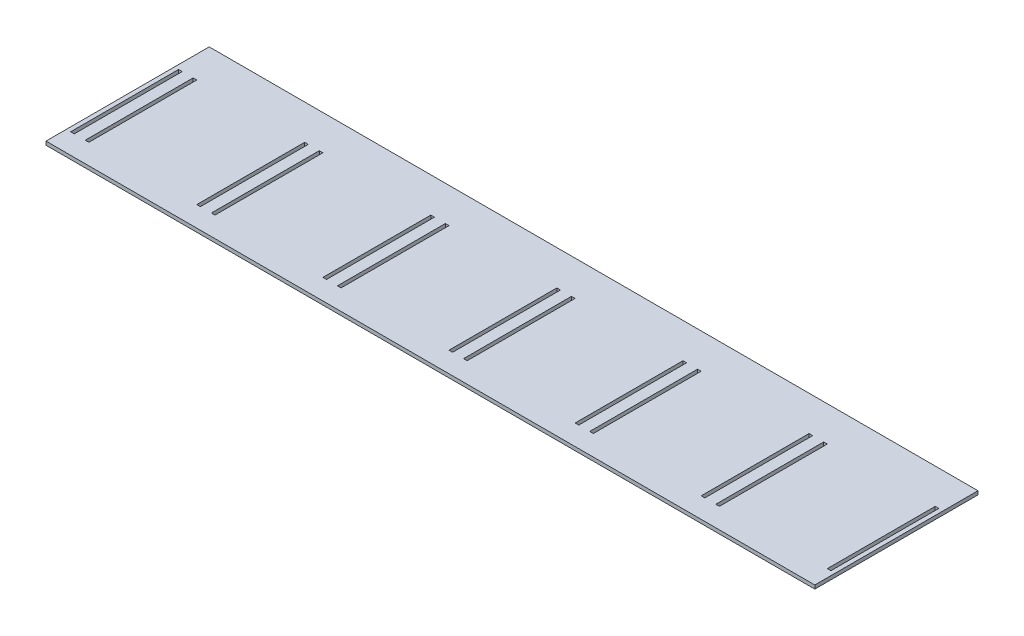
SolidWorks part; units mm, degrees
ref_plane "Front Plane" through (0, 0, 0) normal (0, 0, 1) x (1, 0, 0)
ref_plane "Top Plane" through (0, 0, 0) normal (0, 1, 0) x (1, 0, 0)
ref_plane "Right Plane" through (0, 0, 0) normal (1, 0, 0) x (0, 0, -1)
sketch "Sketch2" plane through (0, 0, 0) normal (0, 1, 0) x (1, 0, 0)
  line L0 (72.7165, -41.1648) -> (74.7165, -41.1648)
  line L2 (70.3665, 37.5852) -> (70.3665, -52.4148)
  line L3 (142.2665, 18.3352) -> (144.2665, 18.3352)
  line L4 (70.3665, 37.5852) -> (494.3665, 37.5852)
  line L5 (70.3665, 41.5852) -> (70.3665, -52.4148) construction
  line L6 (74.7165, 18.3352) -> (74.7165, -41.1648)
  line L7 (142.2665, 18.3352) -> (142.2665, -41.1648)
  line L8 (82.7665, 18.3352) -> (82.7665, -41.1648)
  line L9 (72.7165, 18.3352) -> (74.7165, 18.3352)
  line L10 (80.7665, 18.3352) -> (82.7665, 18.3352)
  line L11 (494.3665, 37.5852) -> (494.3665, -52.4148)
  line L12 (80.7665, -41.1648) -> (82.7665, -41.1648)
  line L13 (144.2665, 18.3352) -> (144.2665, -41.1648)
  line L14 (80.7665, 18.3352) -> (80.7665, -41.1648)
  line L15 (142.2665, -41.1648) -> (144.2665, -41.1648)
  line L16 (150.3165, -41.1648) -> (152.3165, -41.1648)
  line L17 (150.3165, 18.3352) -> (150.3165, -41.1648)
  line L18 (152.3165, 18.3352) -> (152.3165, -41.1648)
  line L19 (150.3165, 18.3352) -> (152.3165, 18.3352)
  line L20 (211.8165, 18.3352) -> (213.8165, 18.3352)
  line L21 (211.8165, 18.3352) -> (211.8165, -41.1648)
  line L22 (213.8165, 18.3352) -> (213.8165, -41.1648)
  line L23 (211.8165, -41.1648) -> (213.8165, -41.1648)
  line L24 (219.8665, -41.1648) -> (221.8665, -41.1648)
  line L25 (219.8665, 18.3352) -> (219.8665, -41.1648)
  line L26 (221.8665, 18.3352) -> (221.8665, -41.1648)
  line L27 (219.8665, 18.3352) -> (221.8665, 18.3352)
  line L28 (281.3665, 18.3352) -> (283.3665, 18.3352)
  line L29 (281.3665, 18.3352) -> (281.3665, -41.1648)
  line L30 (283.3665, 18.3352) -> (283.3665, -41.1648)
  line L31 (281.3665, -41.1648) -> (283.3665, -41.1648)
  line L32 (289.4165, -41.1648) -> (291.4165, -41.1648)
  line L33 (289.4165, 18.3352) -> (289.4165, -41.1648)
  line L34 (291.4165, 18.3352) -> (291.4165, -41.1648)
  line L35 (289.4165, 18.3352) -> (291.4165, 18.3352)
  line L36 (350.9165, 18.3352) -> (352.9165, 18.3352)
  line L37 (350.9165, 18.3352) -> (350.9165, -41.1648)
  line L38 (352.9165, 18.3352) -> (352.9165, -41.1648)
  line L39 (350.9165, -41.1648) -> (352.9165, -41.1648)
  line L40 (358.9665, -41.1648) -> (360.9665, -41.1648)
  line L41 (358.9665, 18.3352) -> (358.9665, -41.1648)
  line L42 (360.9665, 18.3352) -> (360.9665, -41.1648)
  line L43 (358.9665, 18.3352) -> (360.9665, 18.3352)
  line L44 (420.4665, 18.3352) -> (422.4665, 18.3352)
  line L45 (420.4665, 18.3352) -> (420.4665, -41.1648)
  line L46 (422.4665, 18.3352) -> (422.4665, -41.1648)
  line L47 (420.4665, -41.1648) -> (422.4665, -41.1648)
  line L48 (428.5165, -41.1648) -> (430.5165, -41.1648)
  line L49 (428.5165, 18.3352) -> (428.5165, -41.1648)
  line L50 (430.5165, 18.3352) -> (430.5165, -41.1648)
  line L51 (428.5165, 18.3352) -> (430.5165, 18.3352)
  line L52 (490.0165, 18.3352) -> (492.0165, 18.3352)
  line L53 (490.0165, 18.3352) -> (490.0165, -41.1648)
  line L54 (492.0165, 18.3352) -> (492.0165, -41.1648)
  line L55 (490.0165, -41.1648) -> (492.0165, -41.1648)
  line L56 (494.3665, 41.5852) -> (494.3665, -52.4148) construction
  line L60 (72.7165, 18.3352) -> (72.7165, -41.1648)
  line L61 (70.3665, -52.4148) -> (494.3665, -52.4148)
  line L62 (72.7165, 18.3352) -> (72.7165, -41.1648) [skipped]
  line L63 (498.0665, -41.1648) -> (500.0665, -41.1648) [skipped]
  line L64 (498.0665, 18.3352) -> (498.0665, -41.1648) [skipped]
  line L65 (500.0665, 18.3352) -> (500.0665, -41.1648) [skipped]
  line L66 (498.0665, 18.3352) -> (500.0665, 18.3352) [skipped]
  dimension "D1" = 7
extrude "Boss-Extrude1" add sketch "Sketch2" along normal blind 2
